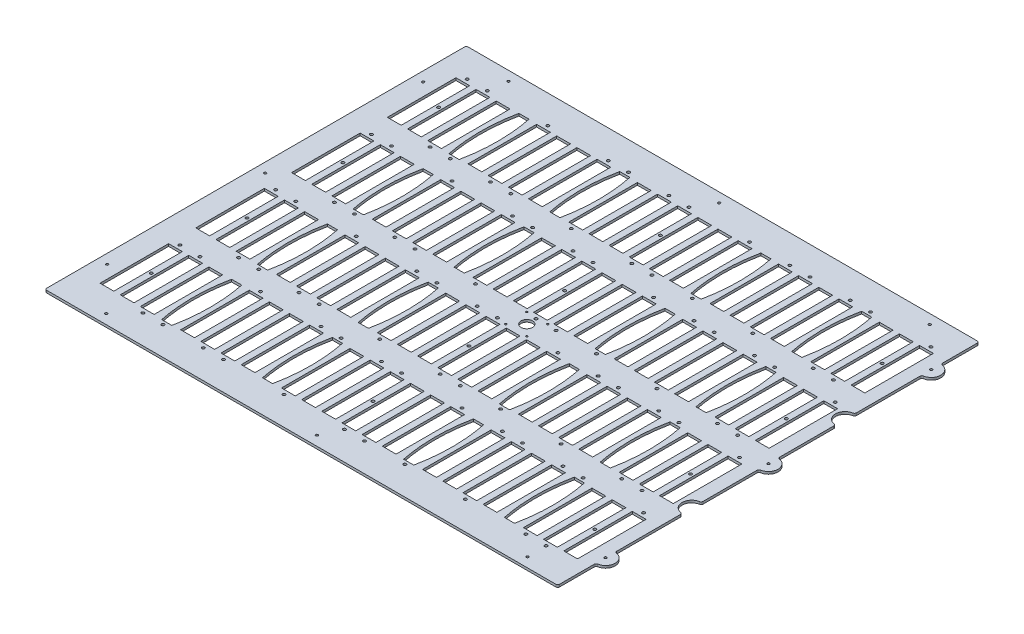
SolidWorks part; units mm, degrees
ref_plane "Front Plane" through (0, 0, 0) normal (0, 0, 1) x (1, 0, 0)
ref_plane "Top Plane" through (0, 0, 0) normal (0, 1, 0) x (1, 0, 0)
ref_plane "Right Plane" through (0, 0, 0) normal (1, 0, 0) x (0, 0, -1)
sketch "Sketch1" plane through (0, 0, 0) normal (0, 1, 0) x (1, 0, 0)
  line L0 (340.1822, 228.7524) -> (340.1822, 279.5524)
  line L1 (-340.1822, -279.5524) -> (340.1822, -279.5524)
  line L2 (-340.1822, -279.5524) -> (-340.1822, 279.5524)
  line L3 (-340.1822, 279.5524) -> (340.1822, 279.5524)
  line L4 (-340.1822, 0) -> (340.2584, 0) construction
  line L5 (-340.1822, -279.5524) -> (340.1822, 279.5524) construction
  line L6 (-340.1822, 279.5524) -> (340.1822, -279.5524) construction
  line L7 (340.1822, 114.4524) -> (340.1822, 203.3524)
  line L8 (340.1822, 12.6998) -> (340.1822, 89.0524)
  line L9 (340.1822, -279.5524) -> (340.1822, -228.7524)
  line L10 (340.1822, -89.0524) -> (340.1822, -12.6998)
  line L11 (340.1822, -203.3524) -> (340.1822, -114.4524)
  arc A0 (340.1822, 203.3524) -> (340.1822, 228.7524) centre (340.1822, 216.0524) ccw
  arc A1 (340.1822, -228.7524) -> (340.1822, -203.3524) centre (340.1822, -216.0524) ccw
  arc A2 (340.1822, -12.6998) -> (340.1822, 12.6998) centre (340.2584, 0) ccw
  arc A3 (340.1822, 114.4524) -> (340.1822, 89.0524) centre (340.1822, 101.7524) ccw
  arc A4 (340.1822, -89.0524) -> (340.1822, -114.4524) centre (340.1822, -101.7524) ccw
  point P0 (0, 0)
  dimension "D3" = 25.4
  dimension "D4" = 63.5
  dimension "D5" = 63.5
  dimension "D6" = 177.8
  dimension "D7" = 177.8
  dimension "D1" = 559.1048
  dimension "D2" = 680.3644
extrude "Boss-Extrude1" add sketch "Sketch1" along normal blind 3.175
sketch "Sketch17" plane through (0, 3.175, 0) normal (0, 1, 0) x (1, 0, 0)
  line L0 (340.1822, 279.5524) -> (-340.1822, 279.5524) construction
  line L1 (-314.7822, 254.1524) -> (327.4822, 254.1524) construction
  line L2 (-314.7822, 254.1524) -> (-314.7822, -254.1524) construction
  line L3 (-314.7822, -254.1524) -> (327.4822, -254.1524) construction
  line L4 (327.4822, 254.1524) -> (327.4822, -254.1524) construction
  line L5 (-340.1822, 279.5524) -> (-340.1822, -279.5524) construction
  line L6 (-340.1822, -279.5524) -> (340.1822, -279.5524) construction
  line L8 (-283.7677, 236.1184) -> (-265.4797, 236.1184)
  line L9 (-310.515, 236.1184) -> (-292.227, 236.1184)
  line L10 (-310.515, 236.1184) -> (-310.515, 145.1864)
  line L11 (-310.515, 145.1864) -> (-292.227, 145.1864)
  line L12 (-292.227, 236.1184) -> (-292.227, 145.1864)
  line L13 (-283.7677, 236.1184) -> (-283.7677, 145.1864)
  line L14 (-265.4797, 236.1184) -> (-265.4797, 145.1864)
  line L15 (-283.7677, 145.1864) -> (-265.4797, 145.1864)
  line L16 (-257.0204, 236.1184) -> (-238.7324, 236.1184)
  line L17 (-257.0204, 236.1184) -> (-257.0204, 145.1864)
  line L18 (-238.7324, 236.1184) -> (-238.7324, 145.1864)
  line L19 (-257.0204, 145.1864) -> (-238.7324, 145.1864)
  line L24 (-203.5258, 236.1184) -> (-185.2378, 236.1184)
  line L25 (-203.5258, 236.1184) -> (-203.5258, 145.1864)
  line L26 (-185.2378, 236.1184) -> (-185.2378, 145.1864)
  line L27 (-203.5258, 145.1864) -> (-185.2378, 145.1864)
  line L28 (-176.7785, 236.1184) -> (-158.4905, 236.1184)
  line L29 (-176.7785, 236.1184) -> (-176.7785, 145.1864)
  line L30 (-158.4905, 236.1184) -> (-158.4905, 145.1864)
  line L31 (-176.7785, 145.1864) -> (-158.4905, 145.1864)
  line L32 (-150.0312, 236.1184) -> (-131.7432, 236.1184)
  line L33 (-150.0312, 236.1184) -> (-150.0312, 145.1864)
  line L34 (-131.7432, 236.1184) -> (-131.7432, 145.1864)
  line L35 (-150.0312, 145.1864) -> (-131.7432, 145.1864)
  line L36 (-123.2839, 236.1184) -> (-104.9959, 236.1184)
  line L37 (-123.2839, 236.1184) -> (-123.2839, 145.1864)
  line L38 (-104.9959, 236.1184) -> (-104.9959, 145.1864)
  line L39 (-123.2839, 145.1864) -> (-104.9959, 145.1864)
  line L44 (-69.7893, 236.1184) -> (-51.5013, 236.1184)
  line L45 (-69.7893, 236.1184) -> (-69.7893, 145.1864)
  line L46 (-51.5013, 236.1184) -> (-51.5013, 145.1864)
  line L47 (-69.7893, 145.1864) -> (-51.5013, 145.1864)
  line L48 (-43.042, 236.1184) -> (-24.754, 236.1184)
  line L49 (-43.042, 236.1184) -> (-43.042, 145.1864)
  line L50 (-24.754, 236.1184) -> (-24.754, 145.1864)
  line L51 (-43.042, 145.1864) -> (-24.754, 145.1864)
  line L52 (-16.2947, 236.1184) -> (1.9933, 236.1184)
  line L53 (-16.2947, 236.1184) -> (-16.2947, 145.1864)
  line L54 (1.9933, 236.1184) -> (1.9933, 145.1864)
  line L55 (-16.2947, 145.1864) -> (1.9933, 145.1864)
  line L56 (10.4527, 236.1184) -> (28.7407, 236.1184)
  line L57 (10.4527, 236.1184) -> (10.4527, 145.1864)
  line L58 (28.7407, 236.1184) -> (28.7407, 145.1864)
  line L59 (10.4527, 145.1864) -> (28.7407, 145.1864)
  line L60 (37.2, 236.1184) -> (55.488, 236.1184)
  line L61 (37.2, 236.1184) -> (37.2, 145.1864)
  line L62 (55.488, 236.1184) -> (55.488, 145.1864)
  line L63 (37.2, 145.1864) -> (55.488, 145.1864)
  line L64 (63.9473, 236.1184) -> (82.2353, 236.1184)
  line L65 (63.9473, 236.1184) -> (63.9473, 145.1864)
  line L66 (82.2353, 236.1184) -> (82.2353, 145.1864)
  line L67 (63.9473, 145.1864) -> (82.2353, 145.1864)
  line L72 (117.4419, 236.1184) -> (135.7299, 236.1184)
  line L73 (117.4419, 236.1184) -> (117.4419, 145.1864)
  line L74 (135.7299, 236.1184) -> (135.7299, 145.1864)
  line L75 (117.4419, 145.1864) -> (135.7299, 145.1864)
  line L76 (144.1892, 236.1184) -> (162.4772, 236.1184)
  line L77 (144.1892, 236.1184) -> (144.1892, 145.1864)
  line L78 (162.4772, 236.1184) -> (162.4772, 145.1864)
  line L79 (144.1892, 145.1864) -> (162.4772, 145.1864)
  line L80 (170.9365, 236.1184) -> (189.2245, 236.1184)
  line L81 (170.9365, 236.1184) -> (170.9365, 145.1864)
  line L82 (189.2245, 236.1184) -> (189.2245, 145.1864)
  line L83 (170.9365, 145.1864) -> (189.2245, 145.1864)
  line L84 (197.6838, 236.1184) -> (215.9718, 236.1184)
  line L85 (197.6838, 236.1184) -> (197.6838, 145.1864)
  line L86 (215.9718, 236.1184) -> (215.9718, 145.1864)
  line L87 (197.6838, 145.1864) -> (215.9718, 145.1864)
  line L92 (251.1784, 236.1184) -> (269.4664, 236.1184)
  line L93 (251.1784, 236.1184) -> (251.1784, 145.1864)
  line L94 (269.4664, 236.1184) -> (269.4664, 145.1864)
  line L95 (251.1784, 145.1864) -> (269.4664, 145.1864)
  line L96 (277.9257, 236.1184) -> (296.2137, 236.1184)
  line L97 (277.9257, 236.1184) -> (277.9257, 145.1864)
  line L98 (296.2137, 236.1184) -> (296.2137, 145.1864)
  line L99 (277.9257, 145.1864) -> (296.2137, 145.1864)
  line L100 (304.673, 236.1184) -> (322.961, 236.1184)
  line L101 (304.673, 236.1184) -> (304.673, 145.1864)
  line L102 (322.961, 236.1184) -> (322.961, 145.1864)
  line L103 (304.673, 145.1864) -> (322.961, 145.1864)
  line L104 (-283.7677, 109.0422) -> (-265.4797, 109.0422)
  line L105 (-283.7677, 109.0422) -> (-283.7677, 18.1102)
  line L106 (-265.4797, 109.0422) -> (-265.4797, 18.1102)
  line L107 (-283.7677, 18.1102) -> (-265.4797, 18.1102)
  line L108 (-257.0204, 109.0422) -> (-238.7324, 109.0422)
  line L109 (-257.0204, 109.0422) -> (-257.0204, 18.1102)
  line L110 (-238.7324, 109.0422) -> (-238.7324, 18.1102)
  line L111 (-257.0204, 18.1102) -> (-238.7324, 18.1102)
  line L116 (-203.5258, 109.0422) -> (-185.2378, 109.0422)
  line L117 (-203.5258, 109.0422) -> (-203.5258, 18.1102)
  line L118 (-185.2378, 109.0422) -> (-185.2378, 18.1102)
  line L119 (-203.5258, 18.1102) -> (-185.2378, 18.1102)
  line L120 (-176.7785, 109.0422) -> (-158.4905, 109.0422)
  line L121 (-176.7785, 109.0422) -> (-176.7785, 18.1102)
  line L122 (-158.4905, 109.0422) -> (-158.4905, 18.1102)
  line L123 (-176.7785, 18.1102) -> (-158.4905, 18.1102)
  line L124 (-150.0312, 109.0422) -> (-131.7432, 109.0422)
  line L125 (-150.0312, 109.0422) -> (-150.0312, 18.1102)
  line L126 (-131.7432, 109.0422) -> (-131.7432, 18.1102)
  line L127 (-150.0312, 18.1102) -> (-131.7432, 18.1102)
  line L128 (-123.2839, 109.0422) -> (-104.9959, 109.0422)
  line L129 (-123.2839, 109.0422) -> (-123.2839, 18.1102)
  line L130 (-104.9959, 109.0422) -> (-104.9959, 18.1102)
  line L131 (-123.2839, 18.1102) -> (-104.9959, 18.1102)
  line L136 (-69.7893, 109.0422) -> (-51.5013, 109.0422)
  line L137 (-69.7893, 109.0422) -> (-69.7893, 18.1102)
  line L138 (-51.5013, 109.0422) -> (-51.5013, 18.1102)
  line L139 (-69.7893, 18.1102) -> (-51.5013, 18.1102)
  line L140 (-43.042, 109.0422) -> (-24.754, 109.0422)
  line L141 (-43.042, 109.0422) -> (-43.042, 18.1102)
  line L142 (-24.754, 109.0422) -> (-24.754, 18.1102)
  line L143 (-43.042, 18.1102) -> (-24.754, 18.1102)
  line L144 (-16.2947, 109.0422) -> (1.9933, 109.0422)
  line L145 (-16.2947, 109.0422) -> (-16.2947, 18.1102)
  line L146 (1.9933, 109.0422) -> (1.9933, 18.1102)
  line L147 (-16.2947, 18.1102) -> (1.9933, 18.1102)
  line L148 (10.4527, 109.0422) -> (28.7407, 109.0422)
  line L149 (10.4527, 109.0422) -> (10.4527, 18.1102)
  line L150 (28.7407, 109.0422) -> (28.7407, 18.1102)
  line L151 (10.4527, 18.1102) -> (28.7407, 18.1102)
  line L152 (37.2, 109.0422) -> (55.488, 109.0422)
  line L153 (37.2, 109.0422) -> (37.2, 18.1102)
  line L154 (55.488, 109.0422) -> (55.488, 18.1102)
  line L155 (37.2, 18.1102) -> (55.488, 18.1102)
  line L156 (63.9473, 109.0422) -> (82.2353, 109.0422)
  line L157 (63.9473, 109.0422) -> (63.9473, 18.1102)
  line L158 (82.2353, 109.0422) -> (82.2353, 18.1102)
  line L159 (63.9473, 18.1102) -> (82.2353, 18.1102)
  line L164 (117.4419, 109.0422) -> (135.7299, 109.0422)
  line L165 (117.4419, 109.0422) -> (117.4419, 18.1102)
  line L166 (135.7299, 109.0422) -> (135.7299, 18.1102)
  line L167 (117.4419, 18.1102) -> (135.7299, 18.1102)
  line L168 (144.1892, 109.0422) -> (162.4772, 109.0422)
  line L169 (144.1892, 109.0422) -> (144.1892, 18.1102)
  line L170 (162.4772, 109.0422) -> (162.4772, 18.1102)
  line L171 (144.1892, 18.1102) -> (162.4772, 18.1102)
  line L172 (170.9365, 109.0422) -> (189.2245, 109.0422)
  line L173 (170.9365, 109.0422) -> (170.9365, 18.1102)
  line L174 (189.2245, 109.0422) -> (189.2245, 18.1102)
  line L175 (170.9365, 18.1102) -> (189.2245, 18.1102)
  line L176 (197.6838, 109.0422) -> (215.9718, 109.0422)
  line L177 (197.6838, 109.0422) -> (197.6838, 18.1102)
  line L178 (215.9718, 109.0422) -> (215.9718, 18.1102)
  line L179 (197.6838, 18.1102) -> (215.9718, 18.1102)
  line L184 (251.1784, 109.0422) -> (269.4664, 109.0422)
  line L185 (251.1784, 109.0422) -> (251.1784, 18.1102)
  line L186 (269.4664, 109.0422) -> (269.4664, 18.1102)
  line L187 (251.1784, 18.1102) -> (269.4664, 18.1102)
  line L188 (277.9257, 109.0422) -> (296.2137, 109.0422)
  line L189 (277.9257, 109.0422) -> (277.9257, 18.1102)
  line L190 (296.2137, 109.0422) -> (296.2137, 18.1102)
  line L191 (277.9257, 18.1102) -> (296.2137, 18.1102)
  line L192 (304.673, 109.0422) -> (322.961, 109.0422)
  line L193 (304.673, 109.0422) -> (304.673, 18.1102)
  line L194 (322.961, 109.0422) -> (322.961, 18.1102)
  line L195 (304.673, 18.1102) -> (322.961, 18.1102)
  line L196 (-283.7677, -18.034) -> (-265.4797, -18.034)
  line L197 (-283.7677, -18.034) -> (-283.7677, -108.966)
  line L198 (-265.4797, -18.034) -> (-265.4797, -108.966)
  line L199 (-283.7677, -108.966) -> (-265.4797, -108.966)
  line L200 (-257.0204, -18.034) -> (-238.7324, -18.034)
  line L201 (-257.0204, -18.034) -> (-257.0204, -108.966)
  line L202 (-238.7324, -18.034) -> (-238.7324, -108.966)
  line L203 (-257.0204, -108.966) -> (-238.7324, -108.966)
  line L208 (-203.5258, -18.034) -> (-185.2378, -18.034)
  line L209 (-203.5258, -18.034) -> (-203.5258, -108.966)
  line L210 (-185.2378, -18.034) -> (-185.2378, -108.966)
  line L211 (-203.5258, -108.966) -> (-185.2378, -108.966)
  line L212 (-176.7785, -18.034) -> (-158.4905, -18.034)
  line L213 (-176.7785, -18.034) -> (-176.7785, -108.966)
  line L214 (-158.4905, -18.034) -> (-158.4905, -108.966)
  line L215 (-176.7785, -108.966) -> (-158.4905, -108.966)
  line L216 (-150.0312, -18.034) -> (-131.7432, -18.034)
  line L217 (-150.0312, -18.034) -> (-150.0312, -108.966)
  line L218 (-131.7432, -18.034) -> (-131.7432, -108.966)
  line L219 (-150.0312, -108.966) -> (-131.7432, -108.966)
  line L220 (-123.2839, -18.034) -> (-104.9959, -18.034)
  line L221 (-123.2839, -18.034) -> (-123.2839, -108.966)
  line L222 (-104.9959, -18.034) -> (-104.9959, -108.966)
  line L223 (-123.2839, -108.966) -> (-104.9959, -108.966)
  line L228 (-69.7893, -18.034) -> (-51.5013, -18.034)
  line L229 (-69.7893, -18.034) -> (-69.7893, -108.966)
  line L230 (-51.5013, -18.034) -> (-51.5013, -108.966)
  line L231 (-69.7893, -108.966) -> (-51.5013, -108.966)
  line L232 (-43.042, -18.034) -> (-24.754, -18.034)
  line L233 (-43.042, -18.034) -> (-43.042, -108.966)
  line L234 (-24.754, -18.034) -> (-24.754, -108.966)
  line L235 (-43.042, -108.966) -> (-24.754, -108.966)
  line L236 (-16.2947, -18.034) -> (1.9933, -18.034)
  line L237 (-16.2947, -18.034) -> (-16.2947, -108.966)
  line L238 (1.9933, -18.034) -> (1.9933, -108.966)
  line L239 (-16.2947, -108.966) -> (1.9933, -108.966)
  line L240 (10.4527, -18.034) -> (28.7407, -18.034)
  line L241 (10.4527, -18.034) -> (10.4527, -108.966)
  line L242 (28.7407, -18.034) -> (28.7407, -108.966)
  line L243 (10.4527, -108.966) -> (28.7407, -108.966)
  line L244 (37.2, -18.034) -> (55.488, -18.034)
  line L245 (37.2, -18.034) -> (37.2, -108.966)
  line L246 (55.488, -18.034) -> (55.488, -108.966)
  line L247 (37.2, -108.966) -> (55.488, -108.966)
  line L248 (63.9473, -18.034) -> (82.2353, -18.034)
  line L249 (63.9473, -18.034) -> (63.9473, -108.966)
  line L250 (82.2353, -18.034) -> (82.2353, -108.966)
  line L251 (63.9473, -108.966) -> (82.2353, -108.966)
  line L256 (117.4419, -18.034) -> (135.7299, -18.034)
  line L257 (117.4419, -18.034) -> (117.4419, -108.966)
  line L258 (135.7299, -18.034) -> (135.7299, -108.966)
  line L259 (117.4419, -108.966) -> (135.7299, -108.966)
  line L260 (144.1892, -18.034) -> (162.4772, -18.034)
  line L261 (144.1892, -18.034) -> (144.1892, -108.966)
  line L262 (162.4772, -18.034) -> (162.4772, -108.966)
  line L263 (144.1892, -108.966) -> (162.4772, -108.966)
  line L264 (170.9365, -18.034) -> (189.2245, -18.034)
  line L265 (170.9365, -18.034) -> (170.9365, -108.966)
  line L266 (189.2245, -18.034) -> (189.2245, -108.966)
  line L267 (170.9365, -108.966) -> (189.2245, -108.966)
  line L268 (197.6838, -18.034) -> (215.9718, -18.034)
  line L269 (197.6838, -18.034) -> (197.6838, -108.966)
  line L270 (215.9718, -18.034) -> (215.9718, -108.966)
  line L271 (197.6838, -108.966) -> (215.9718, -108.966)
  line L276 (251.1784, -18.034) -> (269.4664, -18.034)
  line L277 (251.1784, -18.034) -> (251.1784, -108.966)
  line L278 (269.4664, -18.034) -> (269.4664, -108.966)
  line L279 (251.1784, -108.966) -> (269.4664, -108.966)
  line L280 (277.9257, -18.034) -> (296.2137, -18.034)
  line L281 (277.9257, -18.034) -> (277.9257, -108.966)
  line L282 (296.2137, -18.034) -> (296.2137, -108.966)
  line L283 (277.9257, -108.966) -> (296.2137, -108.966)
  line L284 (304.673, -18.034) -> (322.961, -18.034)
  line L285 (304.673, -18.034) -> (304.673, -108.966)
  line L286 (322.961, -18.034) -> (322.961, -108.966)
  line L287 (304.673, -108.966) -> (322.961, -108.966)
  line L288 (-283.7677, -145.1102) -> (-265.4797, -145.1102)
  line L289 (-283.7677, -145.1102) -> (-283.7677, -236.0422)
  line L290 (-265.4797, -145.1102) -> (-265.4797, -236.0422)
  line L291 (-283.7677, -236.0422) -> (-265.4797, -236.0422)
  line L292 (-257.0204, -145.1102) -> (-238.7324, -145.1102)
  line L293 (-257.0204, -145.1102) -> (-257.0204, -236.0422)
  line L294 (-238.7324, -145.1102) -> (-238.7324, -236.0422)
  line L295 (-257.0204, -236.0422) -> (-238.7324, -236.0422)
  line L300 (-203.5258, -145.1102) -> (-185.2378, -145.1102)
  line L301 (-203.5258, -145.1102) -> (-203.5258, -236.0422)
  line L302 (-185.2378, -145.1102) -> (-185.2378, -236.0422)
  line L303 (-203.5258, -236.0422) -> (-185.2378, -236.0422)
  line L304 (-176.7785, -145.1102) -> (-158.4905, -145.1102)
  line L305 (-176.7785, -145.1102) -> (-176.7785, -236.0422)
  line L306 (-158.4905, -145.1102) -> (-158.4905, -236.0422)
  line L307 (-176.7785, -236.0422) -> (-158.4905, -236.0422)
  line L308 (-150.0312, -145.1102) -> (-131.7432, -145.1102)
  line L309 (-150.0312, -145.1102) -> (-150.0312, -236.0422)
  line L310 (-131.7432, -145.1102) -> (-131.7432, -236.0422)
  line L311 (-150.0312, -236.0422) -> (-131.7432, -236.0422)
  line L312 (-123.2839, -145.1102) -> (-104.9959, -145.1102)
  line L313 (-123.2839, -145.1102) -> (-123.2839, -236.0422)
  line L314 (-104.9959, -145.1102) -> (-104.9959, -236.0422)
  line L315 (-123.2839, -236.0422) -> (-104.9959, -236.0422)
  line L320 (-69.7893, -145.1102) -> (-51.5013, -145.1102)
  line L321 (-69.7893, -145.1102) -> (-69.7893, -236.0422)
  line L322 (-51.5013, -145.1102) -> (-51.5013, -236.0422)
  line L323 (-69.7893, -236.0422) -> (-51.5013, -236.0422)
  line L324 (-43.042, -145.1102) -> (-24.754, -145.1102)
  line L325 (-43.042, -145.1102) -> (-43.042, -236.0422)
  line L326 (-24.754, -145.1102) -> (-24.754, -236.0422)
  line L327 (-43.042, -236.0422) -> (-24.754, -236.0422)
  line L328 (-16.2947, -145.1102) -> (1.9933, -145.1102)
  line L329 (-16.2947, -145.1102) -> (-16.2947, -236.0422)
  line L330 (1.9933, -145.1102) -> (1.9933, -236.0422)
  line L331 (-16.2947, -236.0422) -> (1.9933, -236.0422)
  line L332 (10.4527, -145.1102) -> (28.7407, -145.1102)
  line L333 (10.4527, -145.1102) -> (10.4527, -236.0422)
  line L334 (28.7407, -145.1102) -> (28.7407, -236.0422)
  line L335 (10.4527, -236.0422) -> (28.7407, -236.0422)
  line L336 (37.2, -145.1102) -> (55.488, -145.1102)
  line L337 (37.2, -145.1102) -> (37.2, -236.0422)
  line L338 (55.488, -145.1102) -> (55.488, -236.0422)
  line L339 (37.2, -236.0422) -> (55.488, -236.0422)
  line L340 (63.9473, -145.1102) -> (82.2353, -145.1102)
  line L341 (63.9473, -145.1102) -> (63.9473, -236.0422)
  line L342 (82.2353, -145.1102) -> (82.2353, -236.0422)
  line L343 (63.9473, -236.0422) -> (82.2353, -236.0422)
  line L348 (117.4419, -145.1102) -> (135.7299, -145.1102)
  line L349 (117.4419, -145.1102) -> (117.4419, -236.0422)
  line L350 (135.7299, -145.1102) -> (135.7299, -236.0422)
  line L351 (117.4419, -236.0422) -> (135.7299, -236.0422)
  line L352 (144.1892, -145.1102) -> (162.4772, -145.1102)
  line L353 (144.1892, -145.1102) -> (144.1892, -236.0422)
  line L354 (162.4772, -145.1102) -> (162.4772, -236.0422)
  line L355 (144.1892, -236.0422) -> (162.4772, -236.0422)
  line L356 (170.9365, -145.1102) -> (189.2245, -145.1102)
  line L357 (170.9365, -145.1102) -> (170.9365, -236.0422)
  line L358 (189.2245, -145.1102) -> (189.2245, -236.0422)
  line L359 (170.9365, -236.0422) -> (189.2245, -236.0422)
  line L360 (197.6838, -145.1102) -> (215.9718, -145.1102)
  line L361 (197.6838, -145.1102) -> (197.6838, -236.0422)
  line L362 (215.9718, -145.1102) -> (215.9718, -236.0422)
  line L363 (197.6838, -236.0422) -> (215.9718, -236.0422)
  line L368 (251.1784, -145.1102) -> (269.4664, -145.1102)
  line L369 (251.1784, -145.1102) -> (251.1784, -236.0422)
  line L370 (269.4664, -145.1102) -> (269.4664, -236.0422)
  line L371 (251.1784, -236.0422) -> (269.4664, -236.0422)
  line L372 (277.9257, -145.1102) -> (296.2137, -145.1102)
  line L373 (277.9257, -145.1102) -> (277.9257, -236.0422)
  line L374 (296.2137, -145.1102) -> (296.2137, -236.0422)
  line L375 (277.9257, -236.0422) -> (296.2137, -236.0422)
  line L376 (304.673, -145.1102) -> (322.961, -145.1102)
  line L377 (304.673, -145.1102) -> (304.673, -236.0422)
  line L378 (322.961, -145.1102) -> (322.961, -236.0422)
  line L379 (304.673, -236.0422) -> (322.961, -236.0422)
  line L380 (-310.515, 109.0422) -> (-292.227, 109.0422)
  line L381 (-310.515, 109.0422) -> (-310.515, 18.1102)
  line L382 (-292.227, 109.0422) -> (-292.227, 18.1102)
  line L383 (-310.515, 18.1102) -> (-292.227, 18.1102)
  line L384 (-310.515, -18.034) -> (-292.227, -18.034)
  line L385 (-310.515, -18.034) -> (-310.515, -108.966)
  line L386 (-292.227, -18.034) -> (-292.227, -108.966)
  line L387 (-310.515, -108.966) -> (-292.227, -108.966)
  line L388 (-310.515, -145.1102) -> (-292.227, -145.1102)
  line L389 (-310.515, -145.1102) -> (-310.515, -236.0422)
  line L390 (-292.227, -145.1102) -> (-292.227, -236.0422)
  line L391 (-310.515, -236.0422) -> (-292.227, -236.0422)
  line L392 (340.2584, -279.5524) -> (340.2584, -228.6) construction
  line L393 (340.1822, -203.3524) -> (340.1822, -114.4524) construction
  line L394 (-230.2731, 236.1184) -> (-211.9851, 236.1184) [skipped]
  line L395 (-230.2731, 236.1184) -> (-230.2731, 145.1864) [skipped]
  line L396 (-211.9851, 236.1184) -> (-211.9851, 145.1864) [skipped]
  line L397 (-230.2731, 145.1864) -> (-211.9851, 145.1864) [skipped]
  line L398 (-230.2731, 109.0422) -> (-211.9851, 109.0422) [skipped]
  line L399 (-230.2731, 109.0422) -> (-230.2731, 18.1102) [skipped]
  line L400 (-211.9851, 109.0422) -> (-211.9851, 18.1102) [skipped]
  line L401 (-230.2731, 18.1102) -> (-211.9851, 18.1102) [skipped]
  line L402 (-230.2731, -18.034) -> (-211.9851, -18.034) [skipped]
  line L403 (-230.2731, -18.034) -> (-230.2731, -108.966) [skipped]
  line L404 (-211.9851, -18.034) -> (-211.9851, -108.966) [skipped]
  line L405 (-230.2731, -108.966) -> (-211.9851, -108.966) [skipped]
  line L406 (-230.2731, -145.1102) -> (-211.9851, -145.1102) [skipped]
  line L407 (-230.2731, -145.1102) -> (-230.2731, -236.0422) [skipped]
  line L408 (-211.9851, -145.1102) -> (-211.9851, -236.0422) [skipped]
  line L409 (-230.2731, -236.0422) -> (-211.9851, -236.0422) [skipped]
  line L410 (-96.5366, 236.1184) -> (-78.2486, 236.1184) [skipped]
  line L411 (-96.5366, 236.1184) -> (-96.5366, 145.1864) [skipped]
  line L412 (-78.2486, 236.1184) -> (-78.2486, 145.1864) [skipped]
  line L413 (-96.5366, 145.1864) -> (-78.2486, 145.1864) [skipped]
  line L414 (-96.5366, 109.0422) -> (-78.2486, 109.0422) [skipped]
  line L415 (-96.5366, 109.0422) -> (-96.5366, 18.1102) [skipped]
  line L416 (-78.2486, 109.0422) -> (-78.2486, 18.1102) [skipped]
  line L417 (-96.5366, 18.1102) -> (-78.2486, 18.1102) [skipped]
  line L418 (-96.5366, -18.034) -> (-78.2486, -18.034) [skipped]
  line L419 (-96.5366, -18.034) -> (-96.5366, -108.966) [skipped]
  line L420 (-78.2486, -18.034) -> (-78.2486, -108.966) [skipped]
  line L421 (-96.5366, -108.966) -> (-78.2486, -108.966) [skipped]
  line L422 (-96.5366, -145.1102) -> (-78.2486, -145.1102) [skipped]
  line L423 (-96.5366, -145.1102) -> (-96.5366, -236.0422) [skipped]
  line L424 (-78.2486, -145.1102) -> (-78.2486, -236.0422) [skipped]
  line L425 (-96.5366, -236.0422) -> (-78.2486, -236.0422) [skipped]
  line L426 (90.6946, 236.1184) -> (108.9826, 236.1184) [skipped]
  line L427 (90.6946, 236.1184) -> (90.6946, 145.1864) [skipped]
  line L428 (108.9826, 236.1184) -> (108.9826, 145.1864) [skipped]
  line L429 (90.6946, 145.1864) -> (108.9826, 145.1864) [skipped]
  line L430 (90.6946, 109.0422) -> (108.9826, 109.0422) [skipped]
  line L431 (90.6946, 109.0422) -> (90.6946, 18.1102) [skipped]
  line L432 (108.9826, 109.0422) -> (108.9826, 18.1102) [skipped]
  line L433 (90.6946, 18.1102) -> (108.9826, 18.1102) [skipped]
  line L434 (90.6946, -18.034) -> (108.9826, -18.034) [skipped]
  line L435 (90.6946, -18.034) -> (90.6946, -108.966) [skipped]
  line L436 (108.9826, -18.034) -> (108.9826, -108.966) [skipped]
  line L437 (90.6946, -108.966) -> (108.9826, -108.966) [skipped]
  line L438 (90.6946, -145.1102) -> (108.9826, -145.1102) [skipped]
  line L439 (90.6946, -145.1102) -> (90.6946, -236.0422) [skipped]
  line L440 (108.9826, -145.1102) -> (108.9826, -236.0422) [skipped]
  line L441 (90.6946, -236.0422) -> (108.9826, -236.0422) [skipped]
  line L442 (224.4311, 236.1184) -> (242.7191, 236.1184) [skipped]
  line L443 (224.4311, 236.1184) -> (224.4311, 145.1864) [skipped]
  line L444 (242.7191, 236.1184) -> (242.7191, 145.1864) [skipped]
  line L445 (224.4311, 145.1864) -> (242.7191, 145.1864) [skipped]
  line L446 (224.4311, 109.0422) -> (242.7191, 109.0422) [skipped]
  line L447 (224.4311, 109.0422) -> (224.4311, 18.1102) [skipped]
  line L448 (242.7191, 109.0422) -> (242.7191, 18.1102) [skipped]
  line L449 (224.4311, 18.1102) -> (242.7191, 18.1102) [skipped]
  line L450 (224.4311, -18.034) -> (242.7191, -18.034) [skipped]
  line L451 (224.4311, -18.034) -> (224.4311, -108.966) [skipped]
  line L452 (242.7191, -18.034) -> (242.7191, -108.966) [skipped]
  line L453 (224.4311, -108.966) -> (242.7191, -108.966) [skipped]
  line L454 (224.4311, -145.1102) -> (242.7191, -145.1102) [skipped]
  line L455 (224.4311, -145.1102) -> (224.4311, -236.0422) [skipped]
  line L456 (242.7191, -145.1102) -> (242.7191, -236.0422) [skipped]
  line L457 (224.4311, -236.0422) -> (242.7191, -236.0422) [skipped]
  dimension "D1" = 25.4
  dimension "D2" = 25.4
  dimension "D3" = 25.4
  dimension "D4" = 12.7
  dimension "D5" = 18.288
  dimension "D6" = 90.932
  dimension "D7" = 4.2672
  dimension "D8" = 18.034
  dimension "D9" = 508.3048
  dimension "D10" = 642.2644
  dimension "D11" = 24
  dimension "D13" = 17.2974
  dimension "D14" = 43.5102
  dimension "D12" = 4
extrude "Cut-Extrude5" cut sketch "Sketch17" against normal through all
hole_wizard "#25 (0.1495) Diameter Hole1" positions "Sketch18" profile "Sketch19" hole size "#25" standard "ANSI Inch" end condition through all
sketch "Sketch18" plane through (0, 3.175, 0) normal (0, 1, 0) x (1, 0, 0)
  line L10 (-340.1822, 241.9604) -> (340.1822, 241.9604) construction
  line L11 (-340.1822, 279.5524) -> (-340.1822, -279.5524) construction
  line L12 (340.1822, 228.7524) -> (340.1822, 279.5524) construction
  line L23 (-301.4472, 139.3444) -> (-301.4472, 241.9604) construction
  line L24 (-274.6966, 139.3444) -> (-274.6966, 241.9604) construction
  line L25 (-247.946, 139.3444) -> (-247.946, 241.9604) construction
  line L26 (-221.1954, 139.3444) -> (-221.1954, 241.9604) construction
  line L27 (-194.4448, 139.3444) -> (-194.4448, 241.9604) construction
  line L28 (-167.6941, 139.3444) -> (-167.6941, 241.9604) construction
  line L29 (-140.9435, 139.3444) -> (-140.9435, 241.9604) construction
  line L30 (-114.1929, 139.3444) -> (-114.1929, 241.9604) construction
  line L31 (-87.4423, 139.3444) -> (-87.4423, 241.9604) construction
  line L32 (-60.6917, 139.3444) -> (-60.6917, 241.9604) construction
  line L33 (-33.941, 139.3444) -> (-33.941, 241.9604) construction
  line L34 (-7.1904, 139.3444) -> (-7.1904, 241.9604) construction
  line L35 (19.5602, 139.3444) -> (19.5602, 241.9604) construction
  line L36 (46.3108, 139.3444) -> (46.3108, 241.9604) construction
  line L37 (73.0614, 139.3444) -> (73.0614, 241.9604) construction
  line L38 (99.812, 139.3444) -> (99.812, 241.9604) construction
  line L39 (126.5627, 139.3444) -> (126.5627, 241.9604) construction
  line L40 (153.3133, 139.3444) -> (153.3133, 241.9604) construction
  line L41 (180.0639, 139.3444) -> (180.0639, 241.9604) construction
  line L42 (206.8145, 139.3444) -> (206.8145, 241.9604) construction
  line L43 (233.5651, 139.3444) -> (233.5651, 241.9604) construction
  line L44 (260.3158, 139.3444) -> (260.3158, 241.9604) construction
  line L45 (287.0664, 139.3444) -> (287.0664, 241.9604) construction
  line L46 (313.817, 139.3444) -> (313.817, 241.9604) construction
  line L54 (322.961, -236.0422) -> (322.961, -145.1102) construction
  line L55 (304.673, -236.0422) -> (322.961, -236.0422) construction
  point P259 (-301.4472, 241.9604)
  point P269 (-274.6966, 241.9604)
  point P270 (-247.946, 139.3444)
  point P272 (-221.1954, 139.3444)
  point P275 (-194.4448, 241.9604)
  point P276 (-167.6941, 139.3444)
  point P278 (-140.9435, 139.3444)
  point P281 (-114.1929, 241.9604)
  point P283 (-87.4423, 241.9604)
  point P284 (-60.6917, 139.3444)
  point P287 (-33.941, 241.9604)
  point P289 (-7.1904, 241.9604)
  point P290 (19.5602, 139.3444)
  point P292 (46.3108, 139.3444)
  point P295 (73.0614, 241.9604)
  point P296 (99.812, 139.3444)
  point P299 (126.5627, 241.9604)
  point P301 (153.3133, 241.9604)
  point P302 (180.0639, 139.3444)
  point P305 (206.8145, 241.9604)
  point P307 (233.5651, 241.9604)
  point P308 (260.3158, 139.3444)
  point P310 (287.0664, 139.3444)
  point P313 (313.817, 241.9604)
  point P365 (-301.4472, 114.8842)
  point P366 (-274.6966, 114.8842)
  point P367 (-247.946, 12.2682)
  point P368 (-221.1954, 12.2682)
  point P369 (-194.4448, 114.8842)
  point P370 (-167.6941, 12.2682)
  point P371 (-140.9435, 12.2682)
  point P372 (-114.1929, 114.8842)
  point P373 (-87.4423, 114.8842)
  point P374 (-60.6917, 12.2682)
  point P375 (-33.941, 114.8842)
  point P376 (-7.1904, 114.8842)
  point P377 (19.5602, 12.2682)
  point P378 (46.3108, 12.2682)
  point P379 (73.0614, 114.8842)
  point P380 (99.812, 12.2682)
  point P381 (126.5627, 114.8842)
  point P382 (153.3133, 114.8842)
  point P383 (180.0639, 12.2682)
  point P384 (206.8145, 114.8842)
  point P385 (233.5651, 114.8842)
  point P386 (260.3158, 12.2682)
  point P387 (287.0664, 12.2682)
  point P388 (313.817, 114.8842)
  point P389 (-301.4472, -12.192)
  point P390 (-274.6966, -12.192)
  point P391 (-247.946, -114.808)
  point P392 (-221.1954, -114.808)
  point P393 (-194.4448, -12.192)
  point P394 (-167.6941, -114.808)
  point P395 (-140.9435, -114.808)
  point P396 (-114.1929, -12.192)
  point P397 (-87.4423, -12.192)
  point P398 (-60.6917, -114.808)
  point P399 (-33.941, -12.192)
  point P400 (-7.1904, -12.192)
  point P401 (19.5602, -114.808)
  point P402 (46.3108, -114.808)
  point P403 (73.0614, -12.192)
  point P404 (99.812, -114.808)
  point P405 (126.5627, -12.192)
  point P406 (153.3133, -12.192)
  point P407 (180.0639, -114.808)
  point P408 (206.8145, -12.192)
  point P409 (233.5651, -12.192)
  point P410 (260.3158, -114.808)
  point P411 (287.0664, -114.808)
  point P412 (313.817, -12.192)
  point P413 (-301.4472, -139.2682)
  point P414 (-274.6966, -139.2682)
  point P415 (-247.946, -241.8842)
  point P416 (-221.1954, -241.8842)
  point P417 (-194.4448, -139.2682)
  point P418 (-167.6941, -241.8842)
  point P419 (-140.9435, -241.8842)
  point P420 (-114.1929, -139.2682)
  point P421 (-87.4423, -139.2682)
  point P422 (-60.6917, -241.8842)
  point P423 (-33.941, -139.2682)
  point P424 (-7.1904, -139.2682)
  point P425 (19.5602, -241.8842)
  point P426 (46.3108, -241.8842)
  point P427 (73.0614, -139.2682)
  point P428 (99.812, -241.8842)
  point P429 (126.5627, -139.2682)
  point P430 (153.3133, -139.2682)
  point P431 (180.0639, -241.8842)
  point P432 (206.8145, -139.2682)
  point P433 (233.5651, -139.2682)
  point P434 (260.3158, -241.8842)
  point P435 (287.0664, -241.8842)
  point P436 (313.817, -139.2682)
  dimension "D1" = 9.144
  dimension "D2" = 35.8946
  dimension "D3" = 96.774
  dimension "D4" = 121.2342
  dimension "D5" = 223.8502
sketch "Sketch19" plane through (313.817, 3.175, 139.2682) normal (1, 0, 0) x (0, 0, 1)
  line L0 (0, 0) -> (0, 3.175)
  line L1 (0, 3.175) -> (1.8986, 3.175)
  line L2 (1.8986, 3.175) -> (1.8986, 0)
  line L5 (1.8986, 0) -> (0, 0)
  line L11 (0, -6.35) -> (0, 107.95) construction
  dimension "Thru Hole Dia." = 3.7973
  dimension "Thru Hole Depth" = 3.175
fillet "Fillet1" radius 2.54 14 edges at (-340.1822, 1.5875, -279.5524) (-340.1822, 1.5875, 279.5524) (340.1822, 1.5875, -279.5524) (340.1822, 1.5875, -228.7524) (340.1822, 1.5875, 279.5524) (340.1822, 1.5875, 228.7524) (340.1822, 1.5875, 203.3524) (340.1822, 1.5875, 114.4524) (340.1822, 1.5875, 89.0524) (340.1822, 1.5875, 12.6998) (340.1822, 1.5875, -12.6998) (340.1822, 1.5875, -89.0524) (340.1822, 1.5875, -114.4524) (340.1822, 1.5875, -203.3524)
hole_wizard "#6 Clearance Hole1" positions "Sketch8" profile "Sketch9" hole size "#6" standard "ANSI Inch" end condition through all
sketch "Sketch8" plane through (0, 3.175, 0) normal (0, 1, 0) x (1, 0, 0)
  line L13 (-292.227, 236.1184) -> (-283.7677, 145.1864) construction
  line L15 (1.9933, 236.1184) -> (10.4527, 145.1864) construction
  line L17 (296.2137, 236.1184) -> (304.673, 145.1864) construction
  line L18 (-292.227, 109.0422) -> (-283.7677, 18.1102) construction
  line L19 (1.9933, 109.0422) -> (10.4527, 18.1102) construction
  line L20 (296.2137, 109.0422) -> (304.673, 18.1102) construction
  line L21 (-292.227, -18.034) -> (-283.7677, -108.966) construction
  line L22 (1.9933, -18.034) -> (10.4527, -108.966) construction
  line L23 (296.2137, -18.034) -> (304.673, -108.966) construction
  line L24 (-292.227, -145.1102) -> (-283.7677, -236.0422) construction
  line L25 (1.9933, -145.1102) -> (10.4527, -236.0422) construction
  line L26 (296.2137, -145.1102) -> (304.673, -236.0422) construction
  point P129 (-287.9973, 190.6524)
  point P131 (6.223, 190.6524)
  point P133 (300.4433, 190.6524)
  point P146 (-287.9973, 63.5762)
  point P147 (6.223, 63.5762)
  point P148 (300.4433, 63.5762)
  point P155 (-287.9973, -63.5)
  point P156 (6.223, -63.5)
  point P157 (300.4433, -63.5)
  point P164 (-287.9973, -190.5762)
  point P165 (6.223, -190.5762)
  point P166 (300.4433, -190.5762)
  dimension "D1" = 4
sketch "Sketch9" plane through (300.4433, 3.175, 190.5762) normal (1, 0, 0) x (0, 0, 1)
  line L0 (0, 0) -> (0, 3.175)
  line L1 (0, 3.175) -> (1.8986, 3.175)
  line L2 (1.8986, 3.175) -> (1.8986, 0)
  line L5 (1.8986, 0) -> (0, 0)
  line L11 (0, -6.35) -> (0, 107.95) construction
  dimension "Thru Hole Dia." = 3.7973
  dimension "Thru Hole Depth" = 3.175
hole_wizard "#2 Clearance Hole1" positions "Sketch13" profile "Sketch14" hole size "#2" standard "ANSI Inch" end condition through all
sketch "Sketch13" plane through (0, 3.175, 0) normal (0, 1, 0) x (1, 0, 0)
  line L9 (322.961, -108.966) -> (322.961, -18.034) construction
  line L10 (322.961, -18.034) -> (304.673, -18.034) construction
  line L18 (10.4527, 18.1102) -> (28.7407, -18.034) construction
  line L21 (5.6261, -13.9319) -> (33.5661, -13.9319) construction
  line L22 (5.6261, -13.9319) -> (5.6261, 14.0081) construction
  line L23 (5.6261, 14.0081) -> (33.5661, 14.0081) construction
  line L24 (33.5661, -13.9319) -> (33.5661, 14.0081) construction
  line L25 (5.6261, -13.9319) -> (33.5661, 14.0081) construction
  line L26 (5.6261, 14.0081) -> (33.5661, -13.9319) construction
  line L27 (10.4527, 18.1102) -> (28.7407, 18.1102) construction
  point P129 (5.6261, 14.0081)
  point P132 (5.6261, -13.9319)
  point P135 (33.5661, -13.9319)
  point P138 (33.5661, 14.0081)
  dimension "D1" = 27.94
  dimension "D2" = 27.94
  dimension "D3" = 4.1021
sketch "Sketch14" plane through (33.5661, 3.175, -14.0081) normal (1, 0, 0) x (0, 0, 1)
  line L0 (0, 0) -> (0, 3.175)
  line L1 (0, 3.175) -> (1.2192, 3.175)
  line L2 (1.2192, 3.175) -> (1.2192, 0)
  line L5 (1.2192, 0) -> (0, 0)
  line L11 (0, -6.35) -> (0, 107.95) construction
  dimension "Thru Hole Dia." = 2.4384
  dimension "Thru Hole Depth" = 3.175
sketch "Sketch20" plane through (0, 3.175, 0) normal (0, 1, 0) x (1, 0, 0)
  line L0 (5.6261, 14.0081) -> (33.5661, -13.9319) construction
  circle A0 centre (19.5961, 0.0381) radius 7.62
  dimension "D1" = 15.24
extrude "Cut-Extrude6" cut sketch "Sketch20" against normal through all
hole_wizard "1/8 (0.125) Diameter Hole1" positions "Sketch21" profile "Sketch22" hole size "1/8" standard "ANSI Inch" end condition through all
sketch "Sketch21" plane through (0, 3.175, 0) normal (0, 1, 0) x (1, 0, 0)
  point P0 (287.3502, 266.8524)
  point P12 (287.3502, -266.8524)
  point P15 (7.9502, -266.8524)
  point P18 (-271.4498, -266.8524)
  point P21 (-327.4822, -209.55)
  point P24 (-327.4822, 0)
  point P27 (-327.4822, 209.55)
  point P30 (-271.4498, 266.8524)
  point P33 (7.9502, 266.8524)
  point P48 (340.1822, 216.0524)
  point P51 (340.2584, 0)
  point P54 (340.1822, -216.0524)
sketch "Sketch22" plane through (287.3502, 3.175, -266.8524) normal (1, 0, 0) x (0, 0, 1)
  line L0 (0, 0) -> (0, 3.175)
  line L1 (0, 3.175) -> (1.5875, 3.175)
  line L2 (1.5875, 3.175) -> (1.5875, 0)
  line L5 (1.5875, 0) -> (0, 0)
  line L11 (0, -6.35) -> (0, 107.95) construction
  dimension "Thru Hole Dia." = 3.175
  dimension "Thru Hole Depth" = 3.175
sketch "Sketch23" plane through (0, 3.175, 0) normal (0, 1, 0) x (1, 0, 0)
  line L0 (-94.1236, 237.0074) -> (-80.6616, 237.0074)
  line L1 (-232.5591, 190.6524) -> (-209.6991, 190.6524) construction
  line L2 (-227.8601, 237.0074) -> (-214.3981, 237.0074)
  line L3 (-94.1236, 144.2974) -> (-80.6616, 144.2974)
  line L4 (-227.8601, 144.2974) -> (-214.3981, 144.2974)
  line L5 (226.8441, 144.2974) -> (240.3061, 144.2974)
  line L6 (-227.8601, 237.0074) -> (-214.3981, 144.2974) construction
  line L7 (-227.8601, 144.2974) -> (-214.3981, 237.0074) construction
  line L8 (226.8441, 237.0074) -> (240.3061, 237.0074)
  line L9 (93.1076, 237.0074) -> (106.5696, 237.0074)
  line L10 (93.1076, 144.2974) -> (106.5696, 144.2974)
  line L11 (-227.8601, 109.9312) -> (-214.3981, 109.9312)
  line L12 (-227.8601, 17.2212) -> (-214.3981, 17.2212)
  line L13 (-94.1236, 109.9312) -> (-80.6616, 109.9312)
  line L14 (-94.1236, 17.2212) -> (-80.6616, 17.2212)
  line L15 (226.8441, 17.2212) -> (240.3061, 17.2212)
  line L16 (226.8441, 109.9312) -> (240.3061, 109.9312)
  line L17 (93.1076, 109.9312) -> (106.5696, 109.9312)
  line L18 (93.1076, 17.2212) -> (106.5696, 17.2212)
  line L19 (-227.8601, -17.145) -> (-214.3981, -17.145)
  line L20 (-227.8601, -109.855) -> (-214.3981, -109.855)
  line L21 (-94.1236, -17.145) -> (-80.6616, -17.145)
  line L22 (-94.1236, -109.855) -> (-80.6616, -109.855)
  line L23 (226.8441, -109.855) -> (240.3061, -109.855)
  line L24 (226.8441, -17.145) -> (240.3061, -17.145)
  line L25 (93.1076, -17.145) -> (106.5696, -17.145)
  line L26 (93.1076, -109.855) -> (106.5696, -109.855)
  line L27 (-227.8601, -144.2212) -> (-214.3981, -144.2212)
  line L28 (-227.8601, -236.9312) -> (-214.3981, -236.9312)
  line L29 (-94.1236, -144.2212) -> (-80.6616, -144.2212)
  line L30 (-94.1236, -236.9312) -> (-80.6616, -236.9312)
  line L31 (226.8441, -236.9312) -> (240.3061, -236.9312)
  line L32 (226.8441, -144.2212) -> (240.3061, -144.2212)
  line L33 (93.1076, -144.2212) -> (106.5696, -144.2212)
  line L34 (93.1076, -236.9312) -> (106.5696, -236.9312)
  line L35 (322.961, -108.966) -> (322.961, -18.034) construction
  line L36 (322.961, -18.034) -> (304.673, -18.034) construction
  spline S0 degree 2 poles (-214.3981, 237.0074) (-205.0001, 190.6524) (-214.3981, 144.2974) knots 0 0 0 1 1 1
  spline S1 degree 2 poles (-227.8601, 237.0074) (-237.2581, 190.6524) (-227.8601, 144.2974) knots 0 0 0 1 1 1
  spline S2 degree 2 poles (-94.1236, 237.0074) (-103.5216, 190.6524) (-94.1236, 144.2974) knots 0 0 0 1 1 1
  spline S3 degree 2 poles (-80.6616, 237.0074) (-71.2636, 190.6524) (-80.6616, 144.2974) knots 0 0 0 1 1 1
  spline S4 degree 2 poles (240.3061, 237.0074) (249.7041, 190.6524) (240.3061, 144.2974) knots 0 0 0 1 1 1
  spline S5 degree 2 poles (226.8441, 237.0074) (217.4461, 190.6524) (226.8441, 144.2974) knots 0 0 0 1 1 1
  spline S6 degree 2 poles (93.1076, 237.0074) (83.7096, 190.6524) (93.1076, 144.2974) knots 0 0 0 1 1 1
  spline S7 degree 2 poles (106.5696, 237.0074) (115.9676, 190.6524) (106.5696, 144.2974) knots 0 0 0 1 1 1
  spline S8 degree 2 poles (-214.3981, 109.9312) (-205.0001, 63.5762) (-214.3981, 17.2212) knots 0 0 0 1 1 1
  spline S9 degree 2 poles (-227.8601, 109.9312) (-237.2581, 63.5762) (-227.8601, 17.2212) knots 0 0 0 1 1 1
  spline S10 degree 2 poles (-94.1236, 109.9312) (-103.5216, 63.5762) (-94.1236, 17.2212) knots 0 0 0 1 1 1
  spline S11 degree 2 poles (-80.6616, 109.9312) (-71.2636, 63.5762) (-80.6616, 17.2212) knots 0 0 0 1 1 1
  spline S12 degree 2 poles (240.3061, 109.9312) (249.7041, 63.5762) (240.3061, 17.2212) knots 0 0 0 1 1 1
  spline S13 degree 2 poles (226.8441, 109.9312) (217.4461, 63.5762) (226.8441, 17.2212) knots 0 0 0 1 1 1
  spline S14 degree 2 poles (93.1076, 109.9312) (83.7096, 63.5762) (93.1076, 17.2212) knots 0 0 0 1 1 1
  spline S15 degree 2 poles (106.5696, 109.9312) (115.9676, 63.5762) (106.5696, 17.2212) knots 0 0 0 1 1 1
  spline S16 degree 2 poles (-214.3981, -17.145) (-205.0001, -63.5) (-214.3981, -109.855) knots 0 0 0 1 1 1
  spline S17 degree 2 poles (-227.8601, -17.145) (-237.2581, -63.5) (-227.8601, -109.855) knots 0 0 0 1 1 1
  spline S18 degree 2 poles (-94.1236, -17.145) (-103.5216, -63.5) (-94.1236, -109.855) knots 0 0 0 1 1 1
  spline S19 degree 2 poles (-80.6616, -17.145) (-71.2636, -63.5) (-80.6616, -109.855) knots 0 0 0 1 1 1
  spline S20 degree 2 poles (240.3061, -17.145) (249.7041, -63.5) (240.3061, -109.855) knots 0 0 0 1 1 1
  spline S21 degree 2 poles (226.8441, -17.145) (217.4461, -63.5) (226.8441, -109.855) knots 0 0 0 1 1 1
  spline S22 degree 2 poles (93.1076, -17.145) (83.7096, -63.5) (93.1076, -109.855) knots 0 0 0 1 1 1
  spline S23 degree 2 poles (106.5696, -17.145) (115.9676, -63.5) (106.5696, -109.855) knots 0 0 0 1 1 1
  spline S24 degree 2 poles (-214.3981, -144.2212) (-205.0001, -190.5762) (-214.3981, -236.9312) knots 0 0 0 1 1 1
  spline S25 degree 2 poles (-227.8601, -144.2212) (-237.2581, -190.5762) (-227.8601, -236.9312) knots 0 0 0 1 1 1
  spline S26 degree 2 poles (-94.1236, -144.2212) (-103.5216, -190.5762) (-94.1236, -236.9312) knots 0 0 0 1 1 1
  spline S27 degree 2 poles (-80.6616, -144.2212) (-71.2636, -190.5762) (-80.6616, -236.9312) knots 0 0 0 1 1 1
  spline S28 degree 2 poles (240.3061, -144.2212) (249.7041, -190.5762) (240.3061, -236.9312) knots 0 0 0 1 1 1
  spline S29 degree 2 poles (226.8441, -144.2212) (217.4461, -190.5762) (226.8441, -236.9312) knots 0 0 0 1 1 1
  spline S30 degree 2 poles (93.1076, -144.2212) (83.7096, -190.5762) (93.1076, -236.9312) knots 0 0 0 1 1 1
  spline S31 degree 2 poles (106.5696, -144.2212) (115.9676, -190.5762) (106.5696, -236.9312) knots 0 0 0 1 1 1
  point P4 (-221.1291, 190.6524)
  point P12 (-221.1291, 190.6524)
  dimension "D4" = 2
  dimension "D1" = 92.71
  dimension "D2" = 13.462
  dimension "D3" = 22.86
  dimension "D5" = 2
  dimension "D6" = 4
extrude "Cut-Extrude7" cut sketch "Sketch23" against normal through all
